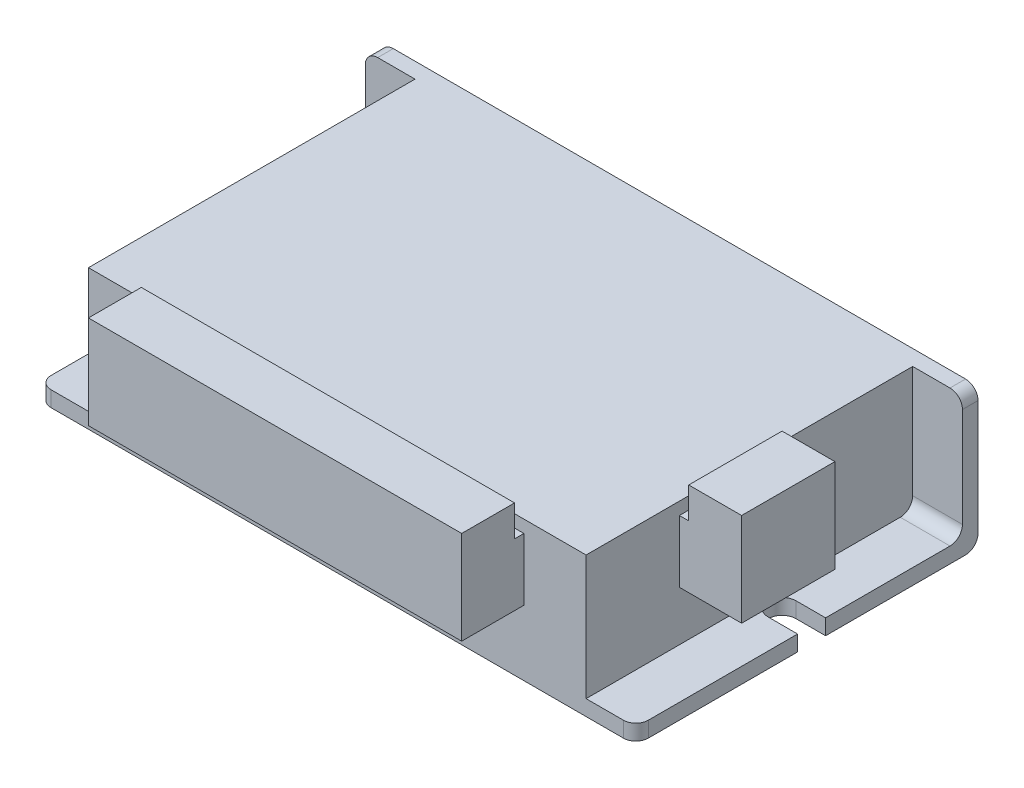
SolidWorks part; units mm, degrees
ref_plane "前视基准面" through (0, 0, 0) normal (0, 0, 1) x (1, 0, 0)
ref_plane "上视基准面" through (0, 0, 0) normal (0, 1, 0) x (1, 0, 0)
ref_plane "右视基准面" through (0, 0, 0) normal (1, 0, 0) x (0, 0, -1)
sketch "草图1" plane through (0, 0, 0) normal (0, 1, 0) x (1, 0, 0)
  line L0 (-40, 27.5) -> (-40, -27.5)
  line L1 (-40, -27.5) -> (40, -27.5)
  line L2 (40, -27.5) -> (40, 27.5)
  line L3 (40, 27.5) -> (-40, 27.5)
  line L4 (0, 27.5) -> (0, -27.5) construction
  line L5 (-40, 0) -> (40, 0) construction
  point P8 (0, 0)
  dimension "D1" = 80
  dimension "D2" = 55
extrude "凸台-拉伸1" add sketch "草图1" along normal blind 20
sketch "草图2" plane through (40, 0, 0) normal (1, 0, 0) x (0, 0, -1)
  line L0 (-12.5, 18) -> (-12.5, 8)
  line L1 (-12.5, 8) -> (2.5, 8)
  line L2 (2.5, 8) -> (2.5, 18)
  line L3 (2.5, 18) -> (-12.5, 18)
  line L4 (27.5, 20) -> (27.5, 0) construction
  line L5 (-27.5, 0) -> (27.5, 0) construction
  dimension "D1" = 15
  dimension "D2" = 10
  dimension "D3" = 25
  dimension "D4" = 8
extrude "凸台-拉伸2" add sketch "草图2" along normal blind 10
sketch "草图3" plane through (0, 18, 0) normal (0, 1, 0) x (1, 0, 0)
  line L0 (50, 2.5) -> (41.5, 2.5)
  line L1 (50, 2.5) -> (40, 2.5) construction
  line L2 (41.5, 2.5) -> (41.5, -12.5)
  line L3 (50, -12.5) -> (40, -12.5) construction
  line L4 (41.5, -12.5) -> (50, -12.5)
  line L5 (50, -12.5) -> (50, 2.5)
  dimension "D1" = 8.5
extrude "凸台-拉伸3" add sketch "草图3" along normal blind 5
sketch "草图4" plane through (0, 0, 27.5) normal (0, 0, 1) x (1, 0, 0)
  line L0 (-30, 18) -> (-30, 8)
  line L2 (-30, 8) -> (30, 8)
  line L3 (30, 8) -> (30, 18)
  line L4 (30, 18) -> (-30, 18)
  line L5 (40, 20) -> (40, 0) construction
  line L6 (41.5, 18) -> (40, 18) construction
  point P8 (0, 0)
  point P9 (0, 0)
  dimension "D1" = 10
  dimension "D2" = 10
  dimension "D3" = 60
extrude "凸台-拉伸4" add sketch "草图4" along normal blind 10
sketch "草图5" plane through (0, 18, 0) normal (0, 1, 0) x (1, 0, 0)
  line L0 (-30, -29) -> (30, -29)
  line L1 (-30, -37.5) -> (-30, -27.5) construction
  line L2 (30, -37.5) -> (30, -27.5) construction
  line L3 (30, -29) -> (30, -37.5)
  line L4 (30, -37.5) -> (-30, -37.5)
  line L5 (-30, -37.5) -> (-30, -29)
  dimension "D1" = 8.5
extrude "凸台-拉伸5" add sketch "草图5" along normal blind 5
sketch "草图6" plane through (0, 0, -27.5) normal (0, 0, -1) x (-1, 0, 0)
  line L0 (-48, 20) -> (48, 20)
  line L1 (-48, 20) -> (-48, 0)
  line L2 (-48, 0) -> (48, 0)
  line L3 (48, 0) -> (48, 20)
  line L4 (-40, 20) -> (-40, 0) construction
  line L5 (40, 20) -> (40, 0) construction
  line L6 (-40, 20) -> (40, 20) construction
  dimension "D1" = 8
  dimension "D2" = 8
extrude "凸台-拉伸6" add sketch "草图6" against normal blind 2.5
sketch "草图7" plane through (0, 0, 0) normal (0, -1, 0) x (1, 0, 0)
  line L0 (-48, -27.5) -> (48, -27.5)
  line L1 (48, -27.5) -> (48, 27.5)
  line L2 (48, 27.5) -> (-48, 27.5)
  line L3 (-48, 27.5) -> (-48, -27.5)
  line L4 (-40, 27.5) -> (40, 27.5) construction
  line L5 (48, -27.5) -> (-48, -27.5) construction
  line L6 (-48, -25) -> (-48, -27.5) construction
  line L7 (48, -25) -> (48, -27.5) construction
  point P8 (0, 0)
  point P9 (0, 0)
extrude "凸台-拉伸8" add sketch "草图7" along normal blind 2.5
fillet "圆角1" radius 2 7 edges at (44, 0, -25) (-44, 0, -25) (0, -2.5, -27.5) (-48, 20, -26.25) (-48, -1.25, 27.5) (48, 20, -26.25) (48, -1.25, 27.5)
sketch "草图8" plane through (0, -2.5, 0) normal (0, -1, 0) x (1, 0, 0)
  line L0 (-48, -3) -> (-43.25, -3)
  line L1 (-48, 25.5) -> (-48, -25.5) construction
  line L2 (0, -25.5) -> (0, 27.5) construction
  line L3 (-43.25, 1.5) -> (-48, 1.5)
  line L4 (-48, 1.5) -> (-48, -3)
  line L5 (46, 27.5) -> (-46, 27.5) construction
  line L7 (-48, -25.5) -> (48, -25.5) construction
  line L8 (48, 1.5) -> (48, -3)
  line L9 (43.25, 1.5) -> (48, 1.5)
  line L10 (48, -3) -> (43.25, -3)
  arc A0 (-43.25, -3) -> (-43.25, 1.5) centre (-43.25, -0.75) ccw
  arc A1 (43.25, -3) -> (43.25, 1.5) centre (43.25, -0.75) cw
  dimension "D3" = 7
  dimension "D1" = 26
  dimension "D2" = 4.5
extrude "切除-拉伸1" cut sketch "草图8" against normal blind 2.5
